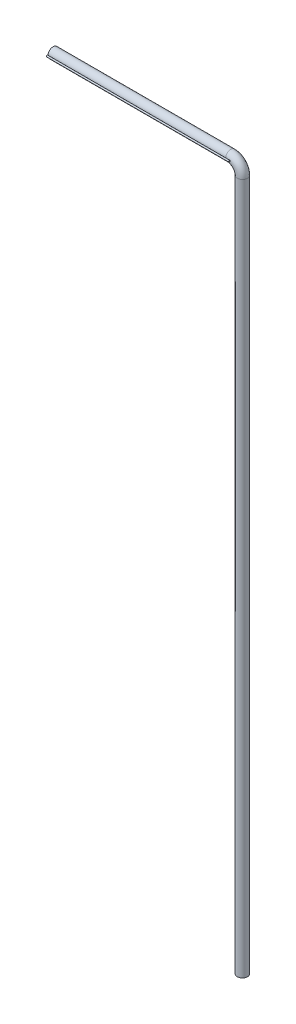
SolidWorks part; units mm, degrees
ref_plane "Alzado" through (0, 0, 0) normal (0, 0, 1) x (1, 0, 0)
ref_plane "Planta" through (0, 0, 0) normal (0, 1, 0) x (1, 0, 0)
ref_plane "Vista lateral" through (0, 0, 0) normal (1, 0, 0) x (0, 0, -1)
sketch "Croquis1" plane through (0, 0, 0) normal (0, 1, 0) x (1, 0, 0)
  circle A1 centre (0, 0) radius 52.8
extrude "Saliente-Extruir2" add sketch "Croquis1" along normal blind 10
sketch "Croquis3" plane through (0, 10, 0) normal (0, 1, 0) x (1, 0, 0)
  circle A0 centre (0, 0) radius 52.8
  circle A1 centre (0, 0) radius 50.8
  dimension "D1" = 2
sketch3d "Croquis3D1"
  line L0 (0, 0, 0) -> (0, 7134, 0)
  line L1 (-120, 7254, 0) -> (-200, 7254, 0)
  arc A0 (0, 7134, 0) -> (-120, 7254, 0) centre (-120, 7134, 0) ccw
  point P6 (0, 7254, 0)
  point P7 (-120, 7134, 120)
  dimension "D3" = 120
  dimension "D1" = 7254
  dimension "D2" = 200
sweep "Barrer1" add profiles "Croquis3" path "Croquis3D1"
sketch "Croquis4" plane through (-200, 0, 0) normal (-1, 0, 0) x (0, 0, 1)
  line L0 (50.8, 7254) -> (-50.8, 7254) construction
  circle A0 centre (0, 7254) radius 50.8 construction
  circle A1 centre (34.2275, 7254) radius 13.7
  circle A3 centre (0.3675, 7254) radius 13.7
  circle A4 centre (-33.4925, 7254) radius 13.7
  dimension "D1" = 27.4
  dimension "D2" = 3
extrude "Saliente-Extruir3" add sketch "Croquis4" along normal blind 1753 separate body
sketch "Croquis5" plane through (-1953, 0, 0) normal (-1, 0, 0) x (0, 0, 1)
  circle A1 centre (0.3675, 6000) radius 13.7
sketch "Croquis7" plane through (-1953, 0, 0) normal (-1, 0, 0) x (0, 0, 1)
  circle A0 centre (34.2275, 7254) radius 13.7
sketch "Croquis8" plane through (-1953, 0, 0) normal (-1, 0, 0) x (0, 0, 1)
  circle A0 centre (-33.4925, 7254) radius 13.7
sketch "Croquis9" plane through (0, 0, 0) normal (0, -1, 0) x (1, 0, 0)
  circle A1 centre (0, 0) radius 50.8
extrude "Cortar-Extruir1" cut sketch "Croquis9" against normal blind 100
sketch "Croquis10" plane through (-200, 0, 0) normal (1, 0, 0) x (0, 0, -1)
  circle A0 centre (33.4925, 7254) radius 13.7
  circle A1 centre (33.4609, 7220.14) radius 13.7
  circle A2 centre (33.4293, 7186.28) radius 13.7
  dimension "D1" = 3
sketch3d "Croquis3D5"
  line L0 (-200, 7254, -33.4925) -> (-73.1414, 7254, -33.4925)
  line L1 (-13.1414, 7194, -33.4925) -> (-13.1414, -26.0228, -33.4925)
  arc A0 (-73.1414, 7254, -33.4925) -> (-13.1414, 7194, -33.4925) centre (-73.1414, 7194, -33.4925) ccw
  point P7 (-13.1414, 7254, -33.4925)
  point P8 (-73.1414, 7194, -93.4925)
  dimension "D1" = 60
ref_plane "Plano1" through (0, 6020, 0) normal (0, 1, 0) x (1, 0, 0)
ref_plane "Plano2" through (0, 0, 0) normal (0, 0, 1) x (1, 0, 0)
sketch "Croquis11" plane through (-200, 0, 0) normal (-1, 0, 0) x (0, 0, 1)
  circle A0 centre (0, 7254) radius 52.8
  circle A1 centre (0, 7254) radius 50.8
extrude "Saliente-Extruir4" add sketch "Croquis11" along normal up to surface (1753 mm away) up to face at (-1953, 7254, 47.9275)
sketch "Croquis12" plane through (-1953, 0, 0) normal (-1, 0, 0) x (0, 0, 1)
  line L0 (20.5285, 7254.1674) -> (91.7103, 7254.1674) construction
  circle A0 centre (34.2275, 7254) radius 13.7 construction
  circle A1 centre (61.7009, 7254.1674) radius 7.9375
  point P6 (61.7009, 7254.1674)
  dimension "D1" = 15.875
extrude "Saliente-Extruir5" add sketch "Croquis12" against normal blind 1880 separate body
